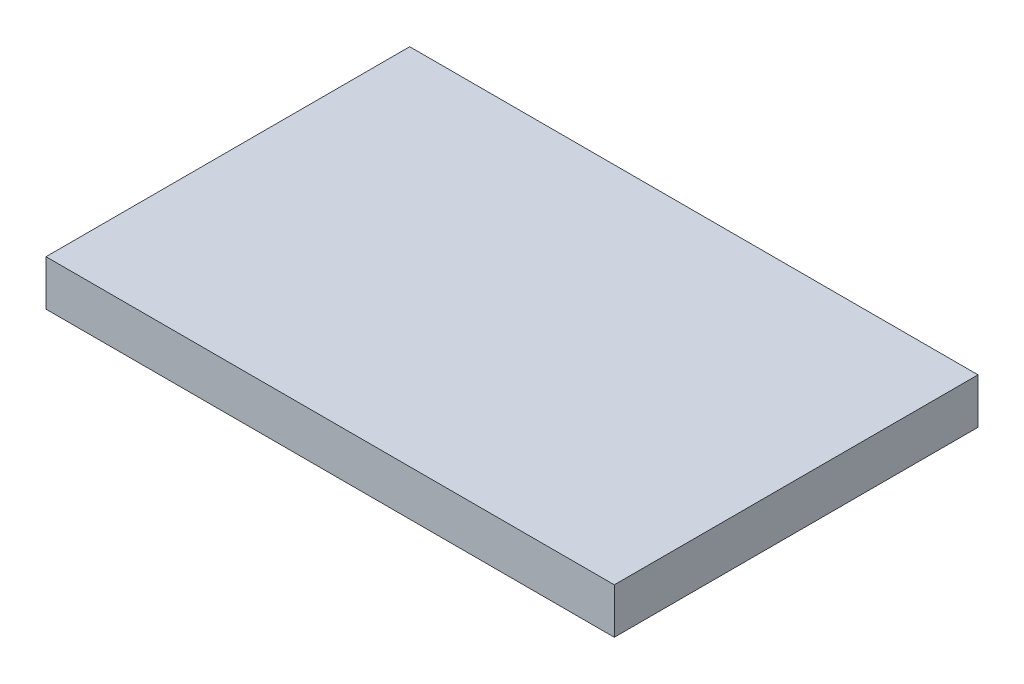
SolidWorks part; units mm, degrees
ref_plane "Front Plane" through (0, 0, 0) normal (0, 0, 1) x (1, 0, 0)
ref_plane "Top Plane" through (0, 0, 0) normal (0, 1, 0) x (1, 0, 0)
ref_plane "Right Plane" through (0, 0, 0) normal (1, 0, 0) x (0, 0, -1)
sketch "Sketch1" plane through (0, 0, 0) normal (0, 0, 1) x (1, 0, 0)
  line L1 (185, 350) -> (-450, 350)
  line L2 (185, 350) -> (185, 299.2)
  line L3 (185, 299.2) -> (-450, 299.2)
  line L4 (-450, 350) -> (-450, 299.2)
  dimension "D1" = 50.8
  dimension "D2" = 635
extrude "Boss-Extrude1" add sketch "Sketch1" along normal blind 406.4
